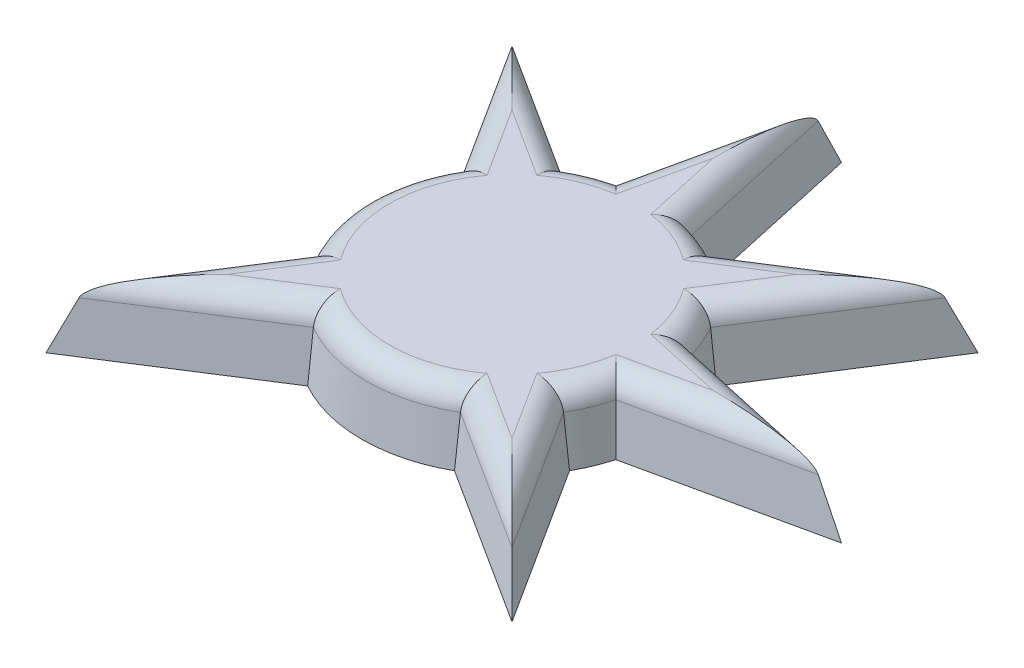
SolidWorks part; units mm, degrees
material "ABS"
ref_plane "Front Plane" through (0, 0, 0) normal (0, 0, 1) x (1, 0, 0)
ref_plane "Top Plane" through (0, 0, 0) normal (0, 1, 0) x (1, 0, 0)
ref_plane "Right Plane" through (0, 0, 0) normal (1, 0, 0) x (0, 0, -1)
sketch "Sketch1" plane through (0, 0, 0) normal (0, 1, 0) x (1, 0, 0)
  line L1 (-17.5, 17.5) -> (17.5, 17.5)
  line L2 (-17.5, 17.5) -> (-17.5, -17.5)
  line L3 (-17.5, -17.5) -> (17.5, -17.5)
  line L4 (17.5, 17.5) -> (17.5, -17.5)
  line L5 (-17.5, 17.5) -> (17.5, -17.5) construction
  line L6 (-17.5, -17.5) -> (17.5, 17.5) construction
  point P0 (0, 0)
  dimension "D1" = 35
sketch "Sketch2" plane through (0, 0, 0) normal (0, 1, 0) x (1, 0, 0)
  line L0 (0, 14.5436) -> (-1.795, 6.3768)
  line L1 (0, 14.5436) -> (0, 6.6246) construction
  line L2 (0, 14.5436) -> (1.795, 6.3768)
  line L3 (10.2839, 10.2839) -> (3.2399, 5.7783)
  line L4 (10.2839, 10.2839) -> (5.7783, 3.2399)
  line L5 (14.5436, 0) -> (6.3768, 1.795)
  line L6 (14.5436, 0) -> (6.3768, -1.795)
  line L7 (10.2839, -10.2839) -> (5.7783, -3.2399)
  line L8 (10.2839, -10.2839) -> (3.2399, -5.7783)
  line L11 (-10.2839, -10.2839) -> (-3.2399, -5.7783)
  line L12 (-10.2839, -10.2839) -> (-5.7783, -3.2399)
  line L15 (-10.2839, 10.2839) -> (-5.7783, 3.2399)
  line L16 (-10.2839, 10.2839) -> (-3.2399, 5.7783)
  line L17 (0, -14.5436) -> (1.795, -6.3768) [skipped]
  line L18 (0, -14.5436) -> (-1.795, -6.3768) [skipped]
  line L19 (-14.5436, 0) -> (-6.3768, -1.795) [skipped]
  line L20 (-14.5436, 0) -> (-6.3768, 1.795) [skipped]
  circle A0 centre (0, 0) radius 6.6246
  point P31 (0, 0)
  dimension "D1" = 8
extrude "Boss-Extrude1" add sketch "Sketch2" along normal blind 3 draft 6
fillet "Fillet1" radius 1 18 edges at (-6.3093, 3, 0) (-7.3272, 3, -6.2466) (-6.2466, 3, -7.3272) (-2.4145, 3, -5.8291) (-0.7641, 3, -9.5981) (0.7641, 3, -9.5981) (2.4145, 3, -5.8291) (6.2466, 3, -7.3272) (7.3272, 3, -6.2466) (5.8291, 3, -2.4145) (9.5981, 3, -0.7641) (9.5981, 3, 0.7641) (5.8291, 3, 2.4145) (7.3272, 3, 6.2466) (6.2466, 3, 7.3272) (0, 3, 6.3093) (-6.2466, 3, 7.3272) (-7.3272, 3, 6.2466)
